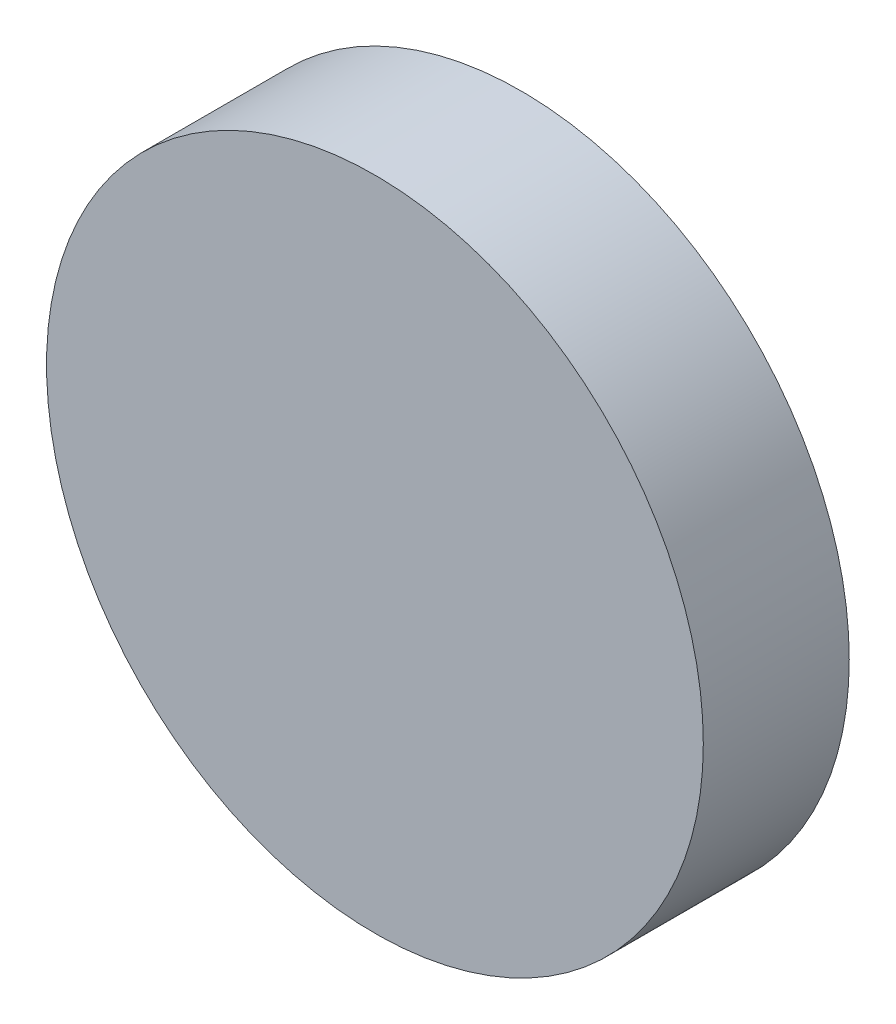
SolidWorks part; units mm, degrees
ref_plane "前视基准面" through (0, 0, 0) normal (0, 0, 1) x (1, 0, 0)
ref_plane "上视基准面" through (0, 0, 0) normal (0, 1, 0) x (1, 0, 0)
ref_plane "右视基准面" through (0, 0, 0) normal (1, 0, 0) x (0, 0, -1)
other "Configuration Table"
sketch "草图1" plane through (0, 0, 0) normal (0, 0, 1) x (1, 0, 0)
  circle A0 centre (-10.5155, 10.3159) radius 22.5
  dimension "D1" = 45
extrude "凸台-拉伸1" add sketch "草图1" along normal blind 10
